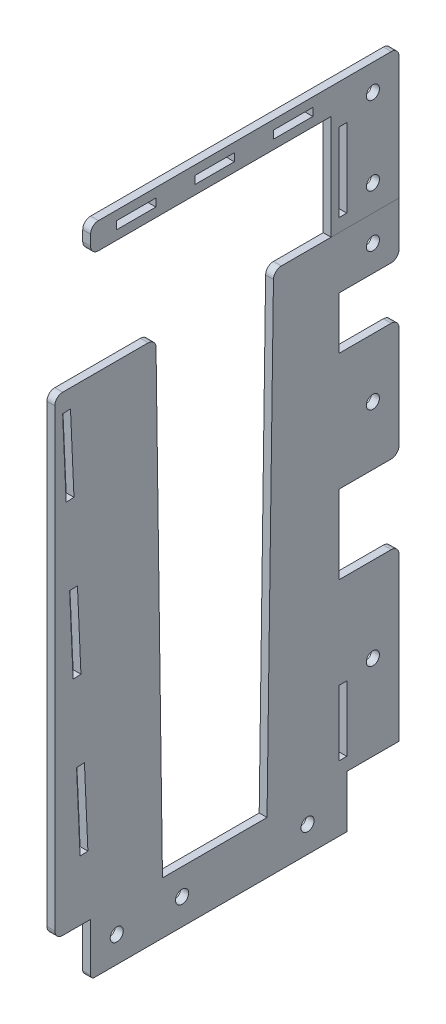
SolidWorks part; units mm, degrees
ref_plane "Front" through (0, 0, 0) normal (0, 0, 1) x (1, 0, 0)
ref_plane "Top" through (0, 0, 0) normal (0, 1, 0) x (1, 0, 0)
ref_plane "Right" through (0, 0, 0) normal (1, 0, 0) x (0, 0, -1)
sketch "Sketch1" plane through (0, 0, 0) normal (1, 0, 0) x (0, 0, -1)
  line L0 (0, 0) -> (-98, 0)
  line L1 (-98, 0) -> (-98, 200)
  line L2 (-98, 200) -> (20, 200)
  line L3 (20, 200) -> (20, 180)
  line L4 (20, 180) -> (-3, 180)
  line L5 (-3, 180) -> (-3, 160)
  line L6 (-3, 160) -> (20, 160)
  line L7 (20, 160) -> (20, 115)
  line L8 (20, 115) -> (-3, 115)
  line L9 (-3, 115) -> (-3, 85)
  line L10 (-3, 85) -> (20, 85)
  line L11 (20, 85) -> (20, 20)
  line L13 (0, 0) -> (0, 20)
  line L14 (0, 20) -> (20, 20)
  line L17 (-3, 50) -> (0, 50)
  line L18 (-3, 50) -> (-3, 25)
  line L19 (-3, 25) -> (0, 25)
  line L20 (0, 50) -> (0, 25)
  circle A0 centre (10, 190) radius 2.5
  circle A1 centre (10, 137.5) radius 2.5
  circle A2 centre (10, 52.5) radius 2.5
  point P4 (-98, 100)
  point P18 (-3, 100)
  point P38 (20, 190)
  point P39 (20, 137.5)
  point P40 (20, 52.5)
  dimension "D6" = 5
  dimension "D10" = 5
  dimension "D11" = 5
  dimension "D12" = 20
  dimension "D14" = 25
  dimension "D15" = 5
  dimension "D1" = 95
  dimension "D2" = 20
  dimension "D3" = 20
  dimension "D4" = 200
  dimension "D5" = 30
  dimension "D7" = 3
  dimension "D8" = 10
  dimension "D9" = 23
  dimension "D13" = 20
extrude "Boss-Extrude1" add sketch "Sketch1" along normal blind 3
sketch "Sketch12" plane through (3, 0, 0) normal (1, 0, 0) x (0, 0, -1)
  line L0 (-98, 200) -> (-98, 0) construction
  line L1 (-98, 0) -> (0, 0) construction
  circle A0 centre (-88, 10) radius 2.5
  dimension "D1" = 5
  dimension "D2" = 10
  dimension "D3" = 10
sketch "Sketch4" plane through (3, 0, 0) normal (1, 0, 0) x (0, 0, -1)
  line L0 (-3, 240) -> (-3, 200)
  line L1 (-3, 250) -> (-98, 250)
  line L2 (-98, 250) -> (-98, 240)
  line L3 (-98, 240) -> (-3, 240)
  line L4 (20, 200) -> (-98, 200) construction
  line L7 (-88, 246.5) -> (-73, 246.5)
  line L8 (-88, 246.5) -> (-88, 243.5)
  line L9 (-88, 243.5) -> (-73, 243.5)
  line L10 (-73, 246.5) -> (-73, 243.5)
  line L11 (-58, 246.5) -> (-43, 246.5)
  line L12 (-58, 246.5) -> (-58, 243.5)
  line L13 (-58, 243.5) -> (-43, 243.5)
  line L14 (-43, 246.5) -> (-43, 243.5)
  line L15 (-28, 246.5) -> (-13, 246.5)
  line L16 (-28, 246.5) -> (-28, 243.5)
  line L17 (-28, 243.5) -> (-13, 243.5)
  line L18 (-13, 246.5) -> (-13, 243.5)
  line L19 (-98, 245) -> (-3, 245) construction
  line L20 (-58, 245) -> (-43, 245) construction
  line L22 (-3, 250) -> (20, 250)
  line L23 (20, 250) -> (20, 200)
  point P29 (-50.5, 245)
  point P30 (-50.5, 245)
  dimension "D1" = 15
  dimension "D2" = 15
  dimension "D3" = 15
  dimension "D4" = 3
  dimension "D5" = 10
  dimension "D7" = 10
  dimension "D8" = 95
  dimension "D6" = 40
  dimension "D9" = 10
  dimension "D10" = 23
extrude "Boss-Extrude2" add sketch "Sketch4" against normal blind 3 separate body
sketch "Sketch5" plane through (3, 0, 0) normal (1, 0, 0) x (0, 0, -1)
  line L0 (-106, 200) -> (-98, 20) construction
  line L1 (-98, 0) -> (0, 0) construction
  line L2 (-105.6882, 192.9853) -> (-108.6853, 192.8521)
  line L3 (-105.6882, 192.9853) -> (-104.3562, 163.0149)
  line L4 (-104.3562, 163.0149) -> (-107.3533, 162.8817)
  line L5 (-108.6853, 192.8521) -> (-107.3533, 162.8817)
  line L6 (-103.0242, 133.0444) -> (-106.0212, 132.9112)
  line L7 (-103.0242, 133.0444) -> (-101.6922, 103.074)
  line L8 (-101.6922, 103.074) -> (-104.6892, 102.9408)
  line L9 (-106.0212, 132.9112) -> (-104.6892, 102.9408)
  line L10 (-100.3602, 73.1036) -> (-103.3572, 72.9704)
  line L11 (-100.3602, 73.1036) -> (-99.0281, 43.1332)
  line L12 (-99.0281, 43.1332) -> (-102.0252, 43)
  line L13 (-103.3572, 72.9704) -> (-102.0252, 43)
  line L16 (20, 200) -> (-98, 200) construction
  line L20 (-98, 200) -> (-111.6853, 200)
  line L21 (-98, 200) -> (-98, 20)
  line L22 (-98, 20) -> (-111.6853, 20)
  line L23 (-111.6853, 200) -> (-111.6853, 20)
  line M27 (-98, 200) -> (-98, 0)
  dimension "D1" = 3
  dimension "D2" = 30
  dimension "D3" = 30
  dimension "D4" = 30
  dimension "D5" = 8
  dimension "D6" = 30
  dimension "D8" = 30
  dimension "D9" = 3
  dimension "D7" = 23
  dimension "D10" = 20
extrude "Boss-Extrude3" add sketch "Sketch5" against normal blind 3 contours L0 L20 L23 L22 L12 L13 L10 L8 L9 L6 L4 L5 L2 | L20 L0 L3 L7 L11 M27
sketch "Sketch6" plane through (3, 0, 0) normal (1, 0, 0) x (0, 0, -1)
  line L0 (-73, 200) -> (-70.5, 20)
  line L1 (20, 200) -> (-111.6853, 200) construction
  line L2 (-70.5, 20) -> (-30.5, 20)
  line L3 (-30.5, 20) -> (-28, 200)
  line L4 (-98, 0) -> (0, 0) construction
  line L5 (-3, 20) -> (-98, 20) construction
  line L6 (-3, 200) -> (-98, 200) construction
  line L7 (20, 200) -> (-111.6853, 200) construction
  line L8 (-73, 200) -> (-28, 200)
  line L9 (-3, 160) -> (-3, 180) construction
  line L11 (-28, 200) -> (-73, 200) construction
  point P16 (-50.5, 20)
  point P19 (-50.5, 20)
  point P22 (-50.5, 200)
  point P23 (-50.5, 200)
  line M29 (20, 200) -> (-111.6853, 200)
  dimension "D1" = 20
  dimension "D2" = 40
  dimension "D3" = 45
  dimension "D4" = 95
extrude "Cut-Extrude3" cut sketch "Sketch6" against normal blind 4 contours L2 L3 L0 M29
fillet "Fillet1" radius 3 8 edges at (1.5, 200, 28) (1.5, 200, 73) (1.5, 180, -20) (1.5, 160, -20) (1.5, 115, -20) (1.5, 85, -20) (1.5, 20, 111.6853) (1.5, 200, 111.6853)
extrude "Cut-Extrude7" cut sketch "Sketch12" against normal blind 4
fillet "Fillet2" radius 1.5 1 edges at (1.5, 0, 98)
sketch "Sketch13" plane through (3, 0, 0) normal (1, 0, 0) x (0, 0, -1)
  line L0 (-88, 10) -> (-1.1076, 10) construction
  line L4 (0, 0) -> (0, 20) construction
  circle A0 centre (-63, 10) radius 2.5
  circle A1 centre (-15, 10) radius 2.5
  point P9 (-78, 10)
  dimension "D1" = 5
  dimension "D2" = 5
  dimension "D3" = 10
  dimension "D4" = 15
  dimension "D5" = 15
extrude "Cut-Extrude8" cut sketch "Sketch13" against normal through all
sketch "Sketch14" [suppressed] plane through (3, 0, 0) normal (1, 0, 0) x (0, 0, -1)
  line L0 (0, 50) -> (23, 50) construction
  line L2 (3, 50) -> (20, 50)
  line L3 (3, 50) -> (3, 20)
  line L4 (3, 20) -> (20, 20)
  line L5 (20, 50) -> (20, 20)
  line L6 (20, 20) -> (20, 85) construction
  line L7 (3, 20) -> (3, 0) construction
  line L8 (-96.5, 0) -> (3, 0) construction
  dimension "D1" = 20
sketch "Sketch15" plane through (3, 0, 0) normal (1, 0, 0) x (0, 0, -1)
  line L0 (-98, 250) -> (20, 250) construction
  line L1 (20, 200) -> (-3, 200) construction
  line L3 (20, 250) -> (20, 200) construction
  circle A0 centre (10, 240) radius 2.5
  circle A1 centre (10, 210) radius 2.5
  dimension "D3" = 10
  dimension "D4" = 5
  dimension "D5" = 5
  dimension "D1" = 10
  dimension "D2" = 10
extrude "Cut-Extrude9" cut sketch "Sketch15" against normal blind 10
sketch "Sketch17" plane through (3, 0, 0) normal (1, 0, 0) x (0, 0, -1)
  line L0 (-3, 240) -> (-3, 200) construction
  line L1 (-3, 235) -> (0, 235)
  line L2 (-3, 235) -> (-3, 205)
  line L3 (-3, 205) -> (0, 205)
  line L4 (0, 235) -> (0, 205)
  line L5 (20, 200) -> (-3, 200) construction
  dimension "D1" = 30
  dimension "D2" = 3
  dimension "D3" = 5
extrude "Cut-Extrude10" cut sketch "Sketch17" against normal through all
sketch "Sketch16" plane through (3, 0, 0) normal (1, 0, 0) x (0, 0, -1)
  line L0 (-98, 240) -> (-3, 240) construction
  line L1 (-6, 240) -> (-3, 240)
  line L2 (-6, 240) -> (-6, 200)
  line L3 (-6, 200) -> (-3, 200)
  line L4 (-3, 240) -> (-3, 200)
  dimension "D1" = 3
extrude "Boss-Extrude4" add sketch "Sketch16" against normal blind 3
fillet "Fillet3" radius 3 3 edges at (1.5, 250, -20) (1.5, 240, 98) (1.5, 250, 98)
equation "\"D2@Sketch4\"=\"D1@Sketch4\""
equation "\"D3@Sketch4\"=\"D1@Sketch4\""
equation "\"D4@Sketch5\"=\"D3@Sketch5\""
equation "\"D2@Sketch5\"=\"D3@Sketch5\""
equation "\"D6@Sketch5\"=\"D8@Sketch5\""
equation "\"D2@Sketch13\"=\"D1@Sketch13\""
equation "\"D5@Sketch13\"=\"D4@Sketch13\""
equation "\"D2@Sketch15\"=\"D1@Sketch15\""
equation "\"D5@Sketch15\"=\"D4@Sketch15\""
